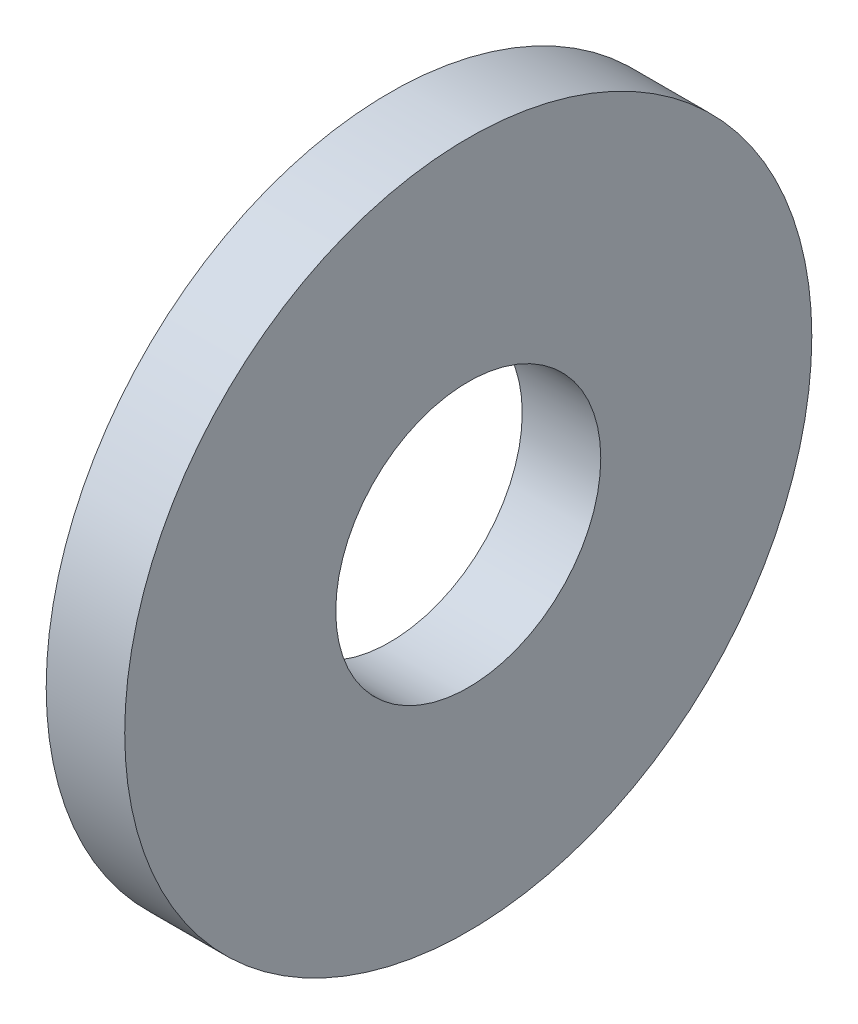
SolidWorks part; units mm, degrees
ref_plane "Plane1" through (0, 0, 0) normal (0, 0, 1) x (1, 0, 0)
ref_plane "Plane2" through (0, 0, 0) normal (0, 1, 0) x (1, 0, 0)
ref_plane "Plane3" through (0, 0, 0) normal (1, 0, 0) x (0, 0, -1)
sketch "Sketch1" plane through (0, 0, 0) normal (1, 0, 0) x (0, 0, -1)
  circle A0 centre (0, 0) radius 2.7
  circle A1 centre (0, 0) radius 7
  dimension "Insid_dia" = 5.4
  dimension "OutsideDia" = 14
extrude "Base-Extrude" add sketch "Sketch1" along normal blind 1.6
